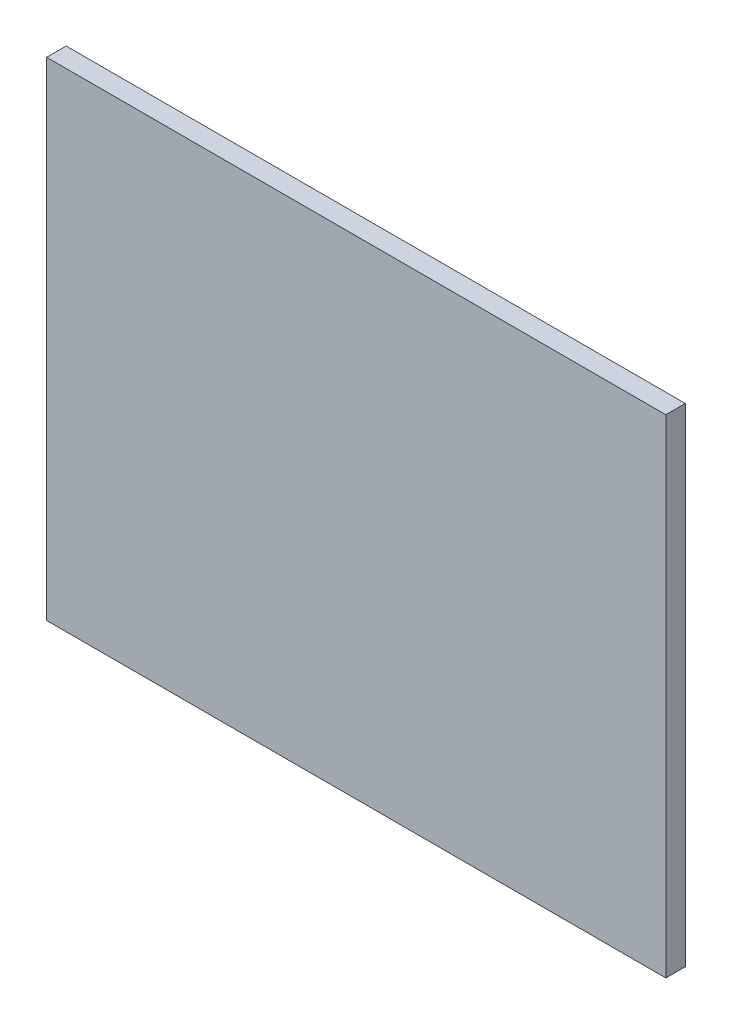
SolidWorks part; units mm, degrees
ref_plane "Ebene vorne" through (0, 0, 0) normal (0, 0, 1) x (1, 0, 0)
ref_plane "Ebene oben" through (0, 0, 0) normal (0, 1, 0) x (1, 0, 0)
ref_plane "Ebene rechts" through (0, 0, 0) normal (1, 0, 0) x (0, 0, -1)
sketch "Skizze1" plane through (0, 0, 0) normal (0, 0, 1) x (1, 0, 0)
  line L1 (301.5, -237.5) -> (-301.5, -237.5)
  line L2 (301.5, -237.5) -> (301.5, 237.5)
  line L3 (301.5, 237.5) -> (-301.5, 237.5)
  line L4 (-301.5, -237.5) -> (-301.5, 237.5)
  line L5 (301.5, -237.5) -> (-301.5, 237.5) construction
  line L6 (301.5, 237.5) -> (-301.5, -237.5) construction
  point P0 (0, 0)
  dimension "D1" = 603
  dimension "D2" = 475
extrude "Aufsatz-Linear austragen1" add sketch "Skizze1" along normal blind 19
